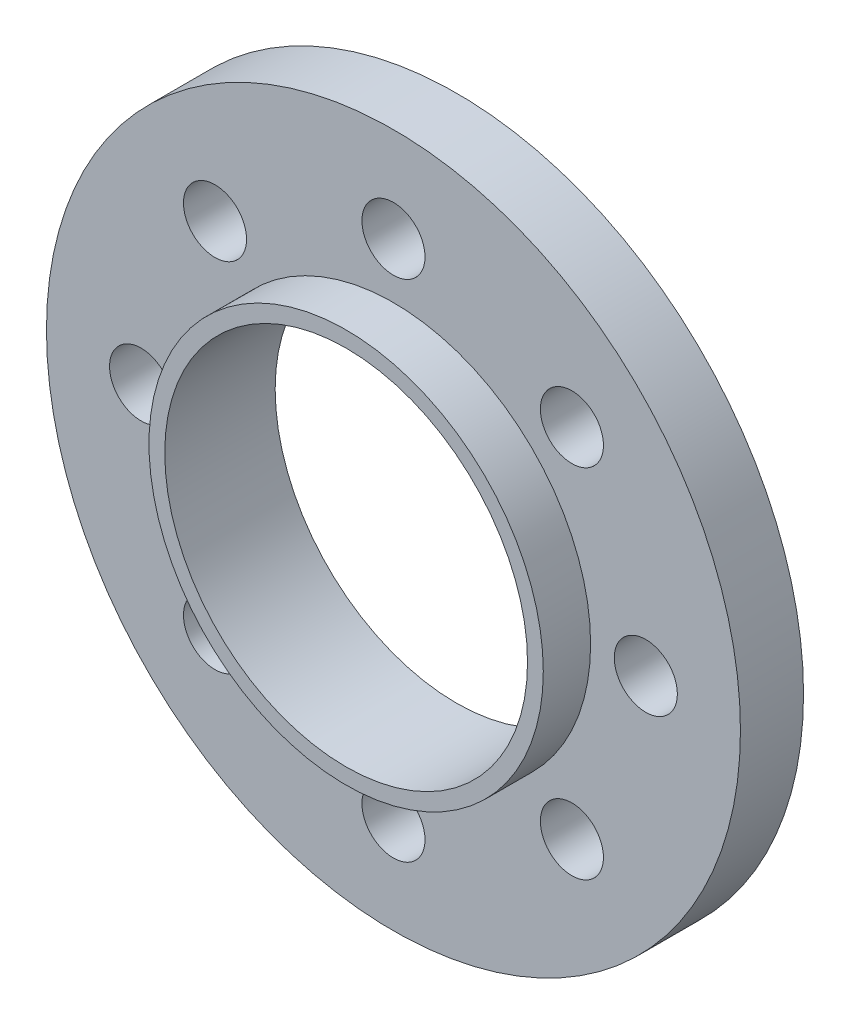
SolidWorks part; units mm, degrees
ref_plane "Front Plane" through (0, 0, 0) normal (0, 0, 1) x (1, 0, 0)
ref_plane "Top Plane" through (0, 0, 0) normal (0, 1, 0) x (1, 0, 0)
ref_plane "Right Plane" through (0, 0, 0) normal (1, 0, 0) x (0, 0, -1)
sketch "Sketch1" plane through (0, 0, 0) normal (0, 0, 1) x (1, 0, 0)
  circle A4 centre (0, 0) radius 11
  circle A5 centre (0, 8) radius 1
  circle A6 centre (5.6569, 5.6569) radius 1
  circle A7 centre (8, 0) radius 1
  circle A8 centre (5.6569, -5.6569) radius 1
  circle A9 centre (0, -8) radius 1
  circle A10 centre (-5.6569, -5.6569) radius 1
  circle A11 centre (-8, 0) radius 1
  circle A12 centre (-5.6569, 5.6569) radius 1
  point P22 (0, 0)
  dimension "D1" = 22
  dimension "D3" = 8
  dimension "D2" = 2
  dimension "D4" = 8
extrude "Boss-Extrude1" add sketch "Sketch1" along normal blind 2
sketch "Sketch2" plane through (0, 0, 2) normal (0, 0, 1) x (1, 0, 0)
  circle A0 centre (0, 0) radius 6.25
  dimension "D1" = 12.5
extrude "Boss-Extrude2" add sketch "Sketch2" along normal blind 1.5
sketch "Sketch3" plane through (0, 0, 3.5) normal (0, 0, 1) x (1, 0, 0)
  circle A0 centre (0, 0) radius 5.75
  dimension "D1" = 11.5
extrude "Cut-Extrude1" cut sketch "Sketch3" against normal blind 11
